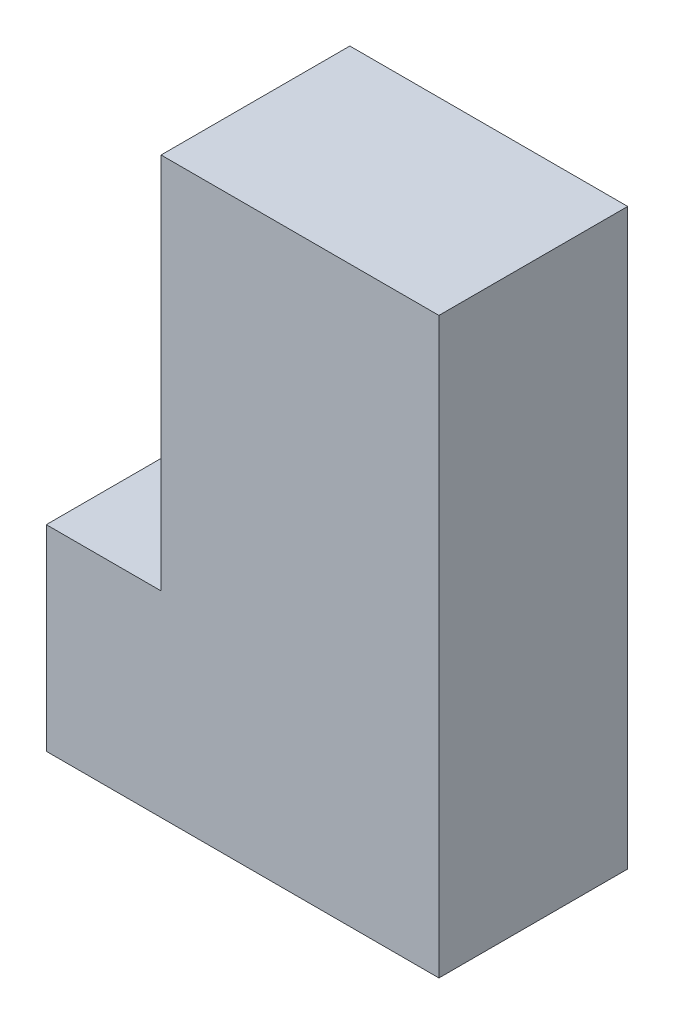
SolidWorks part; units mm, degrees
ref_plane "Front Plane" through (0, 0, 0) normal (0, 0, 1) x (1, 0, 0)
ref_plane "Top Plane" through (0, 0, 0) normal (0, 1, 0) x (1, 0, 0)
ref_plane "Right Plane" through (0, 0, 0) normal (1, 0, 0) x (0, 0, -1)
sketch "Sketch1" plane through (0, 0, 0) normal (0, 0, 1) x (1, 0, 0)
  line L0 (0, 0) -> (26, 0)
  line L1 (26, 0) -> (26, 38)
  line L2 (26, 38) -> (7.6, 38)
  line L3 (7.6, 38) -> (7.6, 13)
  line L4 (7.6, 13) -> (0, 13)
  line L5 (0, 13) -> (0, 0)
  dimension "D1" = 26
  dimension "D2" = 38
  dimension "D3" = 18.4
  dimension "D4" = 13
extrude "Boss-Extrude1" add sketch "Sketch1" along normal blind 12.5
